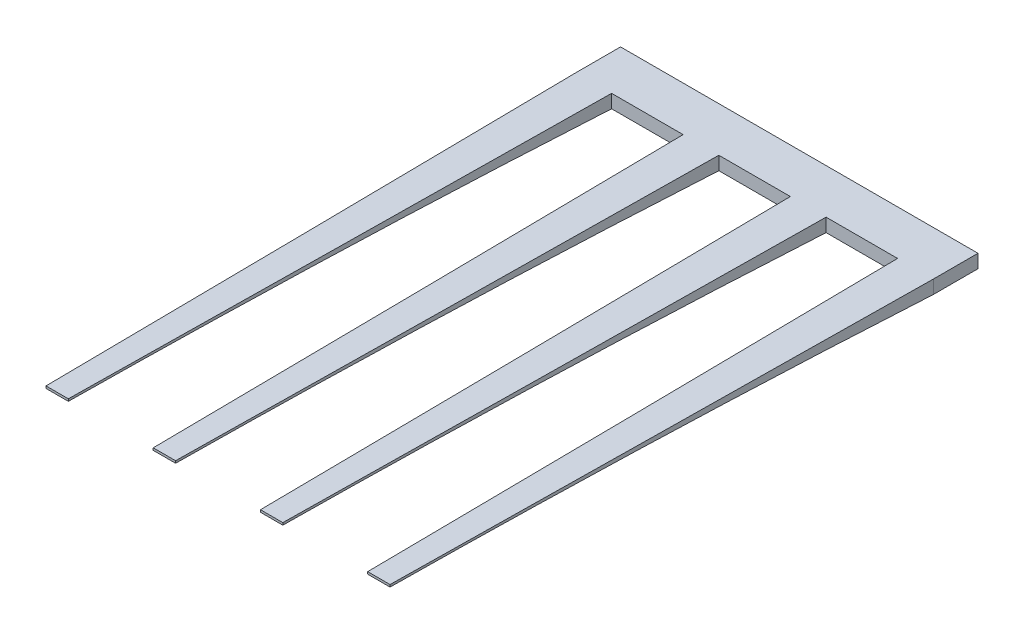
SolidWorks part; units mm, degrees
ref_plane "Front Plane" through (0, 0, 0) normal (0, 0, 1) x (1, 0, 0)
ref_plane "Top Plane" through (0, 0, 0) normal (0, 1, 0) x (1, 0, 0)
ref_plane "Right Plane" through (0, 0, 0) normal (1, 0, 0) x (0, 0, -1)
sketch "Sketch5" plane through (0, 0, 0) normal (0, 0, 1) x (1, 0, 0)
  line L1 (0, 0) -> (1600, 0)
  line L2 (0, 0) -> (0, -60)
  line L3 (0, -60) -> (1600, -60)
  line L4 (1600, 0) -> (1600, -60)
  dimension "D1" = 1600
  dimension "D2" = 60
extrude "Boss-Extrude2" add sketch "Sketch5" along normal blind 200
ref_plane "Plane7" through (0, 0, 1400) normal (0, 0, 1) x (1, 0, 0)
ref_plane "Plane8" through (0, 0, 2600) normal (0, 0, 1) x (1, 0, 0)
sketch "Sketch7" plane through (0, 0, 200) normal (0, 0, 1) x (1, 0, 0)
  line L1 (0, 0) -> (160, 0)
  line L2 (0, 0) -> (0, -60)
  line L3 (0, -60) -> (160, -60)
  line L4 (160, 0) -> (160, -60)
  dimension "D1" = 160
  dimension "D2" = 60
sketch "Sketch9" plane through (0, 0, 1400) normal (0, 0, 1) x (1, 0, 0)
  line L0 (0, 0) -> (160, 0) construction
  line L1 (15, 0) -> (145, 0)
  line L2 (15, 0) -> (15, -20)
  line L3 (15, -20) -> (145, -20)
  line L4 (145, 0) -> (145, -20)
  dimension "D1" = 130
  dimension "D2" = 15
  dimension "D3" = 20
sketch "Sketch10" plane through (0, 0, 2600) normal (0, 0, 1) x (1, 0, 0)
  line L0 (0, 0) -> (160, 0) construction
  line L1 (28.2271, 0) -> (128.2271, 0)
  line L2 (28.2271, 0) -> (28.2271, -10)
  line L3 (28.2271, -10) -> (128.2271, -10)
  line L4 (128.2271, 0) -> (128.2271, -10)
  dimension "D1" = 100
  dimension "D2" = 10
loft "Loft1" add profiles "Sketch7", "Sketch9", "Sketch10"
pattern_linear "LPattern1" count 4 spacing 480 along (-1, 0, 0) of "Loft1"
